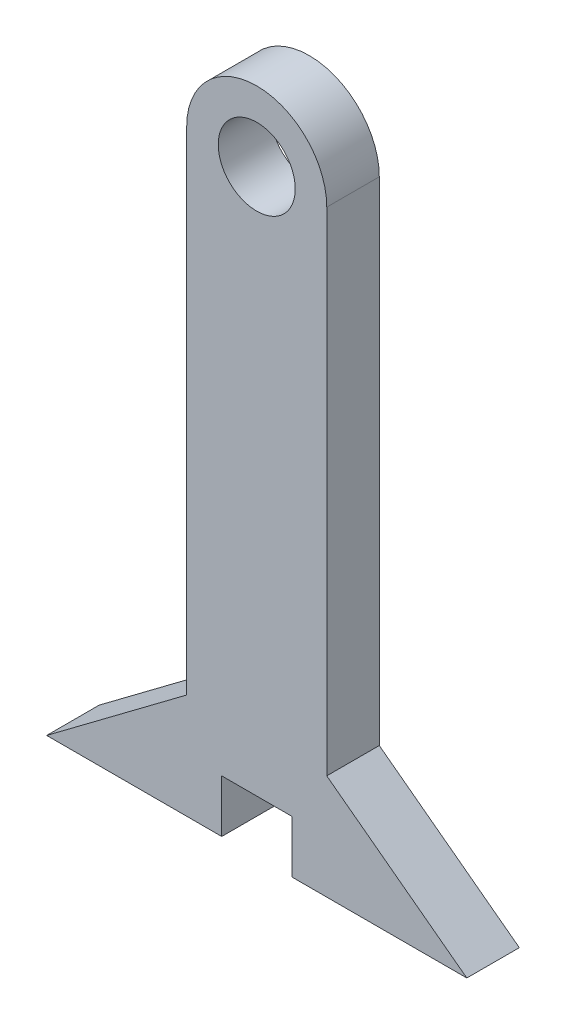
SolidWorks part; units mm, degrees
ref_plane "Alzado" through (0, 0, 0) normal (0, 0, 1) x (1, 0, 0)
ref_plane "Planta" through (0, 0, 0) normal (0, 1, 0) x (1, 0, 0)
ref_plane "Vista lateral" through (0, 0, 0) normal (1, 0, 0) x (0, 0, -1)
sketch "Croquis1" plane through (0, 0, 0) normal (0, 0, 1) x (1, 0, 0)
  line L1 (0, 0) -> (40, 0)
  line L2 (0, 0) -> (0, 170.675)
  line L4 (40, 0) -> (40, 170.675)
  arc A0 (40, 170.675) -> (0, 170.675) centre (20, 170.675) ccw
  circle A1 centre (20, 170.675) radius 11
  dimension "D2" = 40
  dimension "D3" = 22
  dimension "D1" = 170.675
extrude "Saliente-Extruir1" add sketch "Croquis1" along normal mid plane 15
sketch "Croquis2" plane through (0, 0, 7.5) normal (0, 0, 1) x (1, 0, 0)
  line L0 (0, 0) -> (40, 0) construction
  line L1 (10, -15) -> (30, -15)
  line L2 (10, -15) -> (10, 15)
  line L3 (10, 15) -> (30, 15)
  line L4 (30, -15) -> (30, 15)
  line L5 (10, -15) -> (30, 15) construction
  line L6 (10, 15) -> (30, -15) construction
  point P0 (20, 0)
  dimension "D1" = 30
  dimension "D2" = 20
extrude "Cortar-Extruir1" cut sketch "Croquis2" against normal through all
sketch "Croquis3" plane through (0, 0, 7.5) normal (0, 0, 1) x (1, 0, 0)
  line L0 (40, 30) -> (80, 0)
  line L1 (40, 0) -> (40, 170.675) construction
  line L2 (80, 0) -> (40, 0)
  line L3 (40, 30) -> (40, 0)
  line L4 (20, 15) -> (20, 115.1085) construction
  line L5 (30, 15) -> (10, 15) construction
  line L6 (0, 30) -> (0, 0)
  line L7 (-40, 0) -> (0, 0)
  line L8 (0, 30) -> (-40, 0)
  dimension "D1" = 40
  dimension "D2" = 30
extrude "Saliente-Extruir2" add sketch "Croquis3" against normal blind 15
